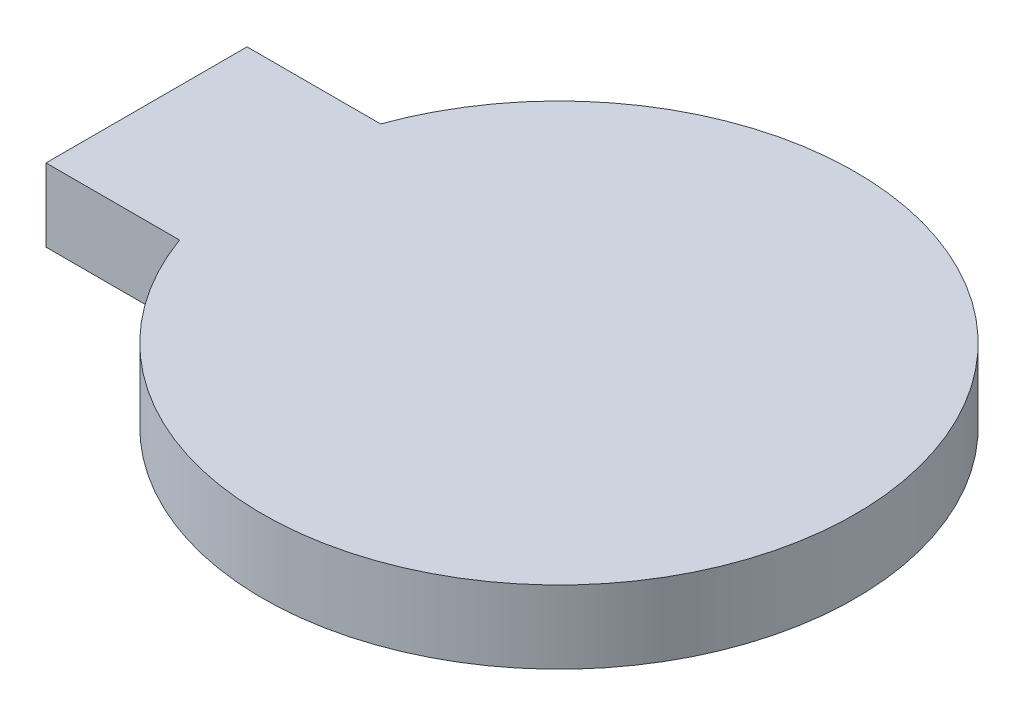
SolidWorks part; units mm, degrees
ref_plane "前视基准面" through (0, 0, 0) normal (0, 0, 1) x (1, 0, 0)
ref_plane "上视基准面" through (0, 0, 0) normal (0, 1, 0) x (1, 0, 0)
ref_plane "右视基准面" through (0, 0, 0) normal (1, 0, 0) x (0, 0, -1)
sketch "草图1" plane through (0, 0, 0) normal (0, 1, 0) x (1, 0, 0)
  line L1 (-16, 3.9) -> (-10.8185, 3.9)
  line L2 (-16, 3.9) -> (-16, -3.9)
  line L3 (-16, -3.9) -> (-10.8185, -3.9)
  arc A0 (-10.8185, -3.9) -> (-10.8185, 3.9) centre (0, 0) ccw
  point P3 (-6.1004, 0)
  dimension "D1" = 23
  dimension "D2" = 7.8
  dimension "D3" = 16
  dimension "D4" = 3.9
extrude "凸台-拉伸1" add sketch "草图1" along normal blind 2.83
sketch "草图2" plane through (0, 0, 0) normal (0, -1, 0) x (1, 0, 0)
  circle A0 centre (0, 0) radius 7.92
  dimension "D1" = 15.84
extrude "凸台-拉伸2" add sketch "草图2" along normal blind 1.5
